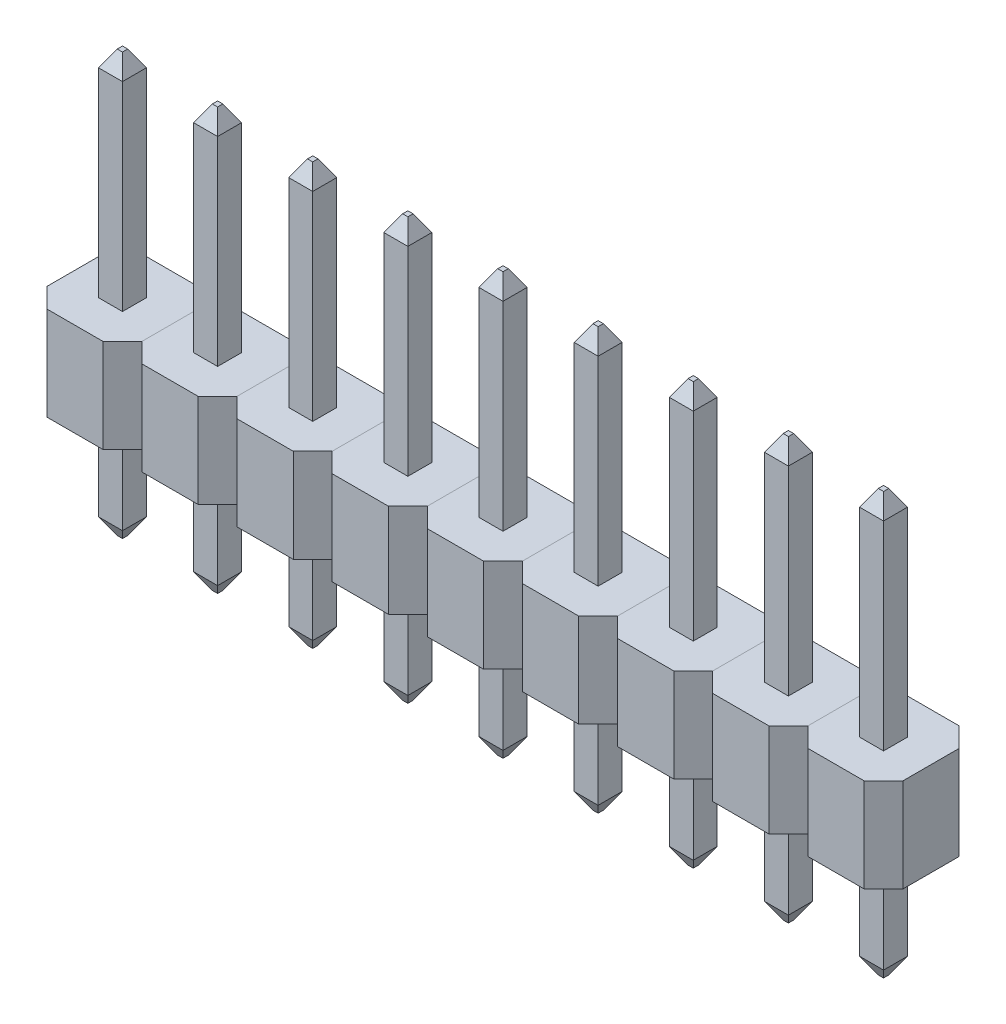
SolidWorks part; units mm, degrees
other "Plastic Body"
other "Metal Pin"
material "ABS"
ref_plane "Front Plane" through (0, 0, 0) normal (0, 0, 1) x (1, 0, 0)
ref_plane "Top Plane" through (0, 0, 0) normal (0, 1, 0) x (1, 0, 0)
ref_plane "Right Plane" through (0, 0, 0) normal (1, 0, 0) x (0, 0, -1)
sketch "Sketch1" plane through (0, 0, 0) normal (0, 1, 0) x (1, 0, 0)
  line L0 (0, 1.27) -> (0, -1.27) construction
  line L1 (-1.27, 1.27) -> (1.27, 1.27)
  line L2 (-1.27, 1.27) -> (-1.27, -1.27)
  line L3 (-1.27, -1.27) -> (1.27, -1.27)
  line L4 (1.27, 1.27) -> (1.27, -1.27)
  line L6 (-0.32, 0.32) -> (0.32, 0.32)
  line L7 (-0.32, 0.32) -> (-0.32, -0.32)
  line L8 (-0.32, -0.32) -> (0.32, -0.32)
  line L9 (0.32, 0.32) -> (0.32, -0.32)
  line L10 (-0.32, 0.32) -> (0.32, -0.32) construction
  line L11 (-0.32, -0.32) -> (0.32, 0.32) construction
  point P7 (0, 0)
  dimension "D1" = 2.54
  dimension "D2" = 2.54
  dimension "D3" = 0.64
extrude "Plastic Connection Body" add sketch "Sketch1" along normal blind 2.5
sketch "Sketch3" plane through (0, 2.5, 0) normal (0, 1, 0) x (1, 0, 0)
  line L5 (0, 1.27) -> (0, -1.27) construction
  line L6 (1.27, 1.27) -> (-1.27, 1.27) construction
  line L7 (-1.27, 0) -> (1.27, 0) construction
  line L8 (-1.27, 1.27) -> (-1.27, -1.27) construction
  line L9 (-0.75, 1.27) -> (0.75, 1.27) construction
  line L10 (-0.75, -1.27) -> (0.75, -1.27) construction
  line L11 (-1.27, 0.75) -> (-1.27, -0.75) construction
  line L12 (1.27, 0.75) -> (1.27, -0.75) construction
  line L13 (-0.75, 1.27) -> (-1.27, 0.75)
  line L14 (-1.27, 0.75) -> (-1.27, 1.27)
  line L15 (-1.27, 1.27) -> (-0.75, 1.27)
  line L16 (0.75, 1.27) -> (1.27, 0.75)
  line L17 (1.27, 0.75) -> (1.27, 1.27)
  line L18 (1.27, 1.27) -> (0.75, 1.27)
  line L19 (-1.27, -0.75) -> (-1.27, -1.27)
  line L20 (-1.27, -1.27) -> (-0.75, -1.27)
  line L21 (-0.75, -1.27) -> (-1.27, -0.75)
  line L22 (0.75, -1.27) -> (1.27, -0.75)
  line L23 (1.27, -0.75) -> (1.27, -1.27)
  line L24 (1.27, -1.27) -> (0.75, -1.27)
  dimension "D1" = 1.5
extrude "Corners Trimmed" cut sketch "Sketch3" against normal up to surface (2.5 mm away) up to face at (0, 0, 0)
sketch "Sketch4" plane through (0, 0, 0) normal (0, -1, 0) x (1, 0, 0)
  line L0 (-0.32, -0.32) -> (-0.32, 0.32) construction
  line L1 (-0.32, 0.32) -> (0.32, 0.32) construction
  line L2 (0.32, -0.32) -> (0.32, 0.32) construction
  line L3 (-0.32, -0.32) -> (0.32, -0.32) construction
  line L4 (-0.32, -0.32) -> (-0.32, 0.32)
  line L5 (-0.32, 0.32) -> (0.32, 0.32)
  line L6 (0.32, -0.32) -> (0.32, 0.32)
  line L7 (-0.32, -0.32) -> (0.32, -0.32)
extrude "Metal Pin" add sketch "Sketch4" along normal blind 3 and the other way blind 8.25 separate body
chamfer "Metal Pin Chamfer-1" distance 0.25 angle 60 4 edges at (-0.32, -3, 0) (0, -3, 0.32) (0.32, -3, 0) (0, -3, -0.32)
chamfer "Metal Pin Chamfer-2" distance 0.25 angle 60 4 edges at (0.32, 8.25, 0) (0, 8.25, 0.32) (-0.32, 8.25, 0) (0, 8.25, -0.32)
sketch "Sketch5" plane through (0, 0, 0) normal (0, -1, 0) x (1, 0, 0)
  circle A0 centre (0, 0) radius 0.5
  dimension "D1" = 1
extrude "Cut-Extrude1" cut sketch "Sketch5" against normal blind 0.1
pattern_linear "LPattern-1" count 5 spacing 2.54 along (1, 0, 0) count 5 spacing 2.54 along (-1, 0, 0) of bodies 217 199 102
